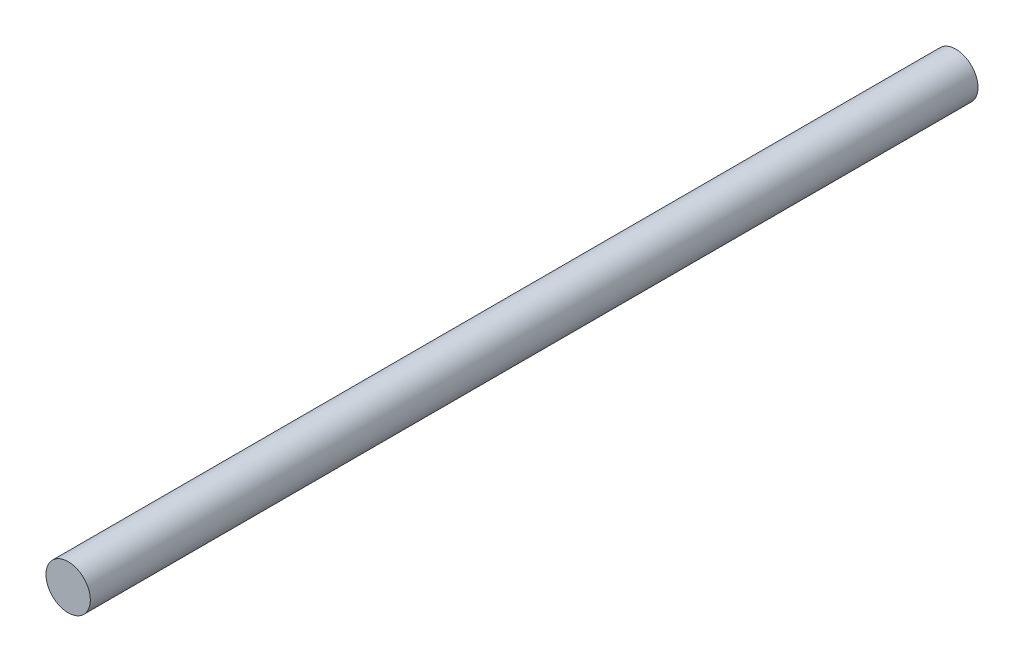
SolidWorks part; units mm, degrees
ref_plane "Plan de face" through (0, 0, 0) normal (0, 0, 1) x (1, 0, 0)
ref_plane "Plan de dessus" through (0, 0, 0) normal (0, 1, 0) x (1, 0, 0)
ref_plane "Plan de droite" through (0, 0, 0) normal (1, 0, 0) x (0, 0, -1)
sketch "Esquisse1" plane through (0, 0, 0) normal (0, 0, 1) x (1, 0, 0)
  circle A0 centre (0, 0) radius 1.5
  dimension "D1" = 3
extrude "Boss.-Extru.1" add sketch "Esquisse1" along normal blind 60
